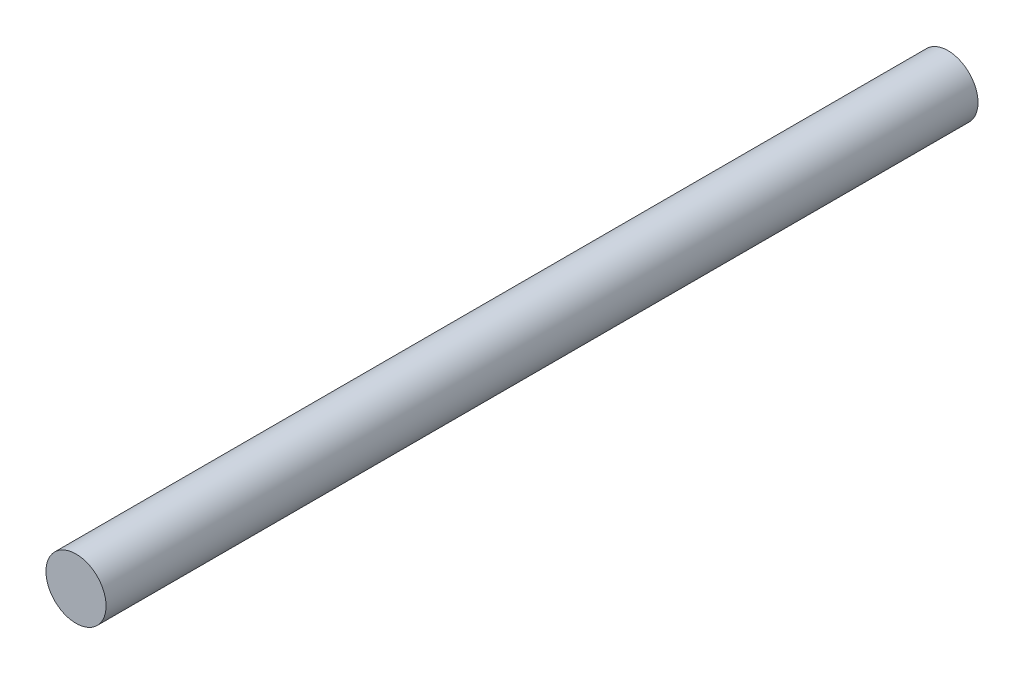
SolidWorks part; units mm, degrees
material "1.4301 (X5CrNi18-10)"
ref_plane "正面" through (0, 0, 0) normal (0, 0, 1) x (1, 0, 0)
ref_plane "平面" through (0, 0, 0) normal (0, 1, 0) x (1, 0, 0)
ref_plane "右側面" through (0, 0, 0) normal (1, 0, 0) x (0, 0, -1)
sketch "ｽｹｯﾁ1" plane through (0, 0, 0) normal (0, 0, 1) x (1, 0, 0)
  circle A0 centre (0, 0) radius 5
  dimension "D1" = 10
extrude "ﾎﾞｽ - 押し出し1" add sketch "ｽｹｯﾁ1" along normal blind 145
